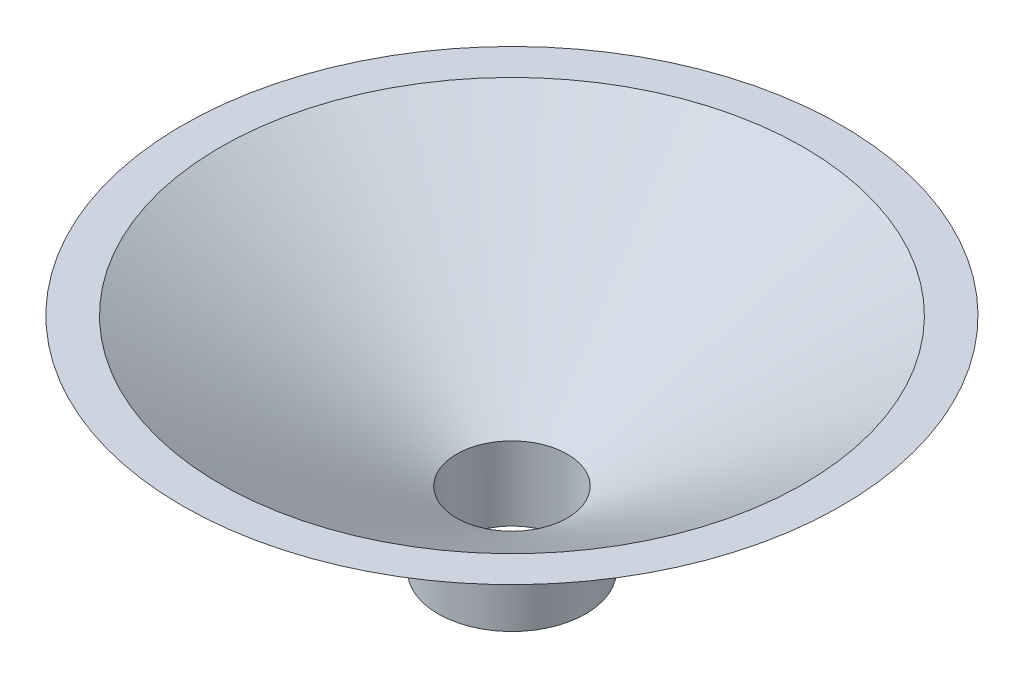
SolidWorks part; units mm, degrees
ref_plane "Front Plane" through (0, 0, 0) normal (0, 0, 1) x (1, 0, 0)
ref_plane "Top Plane" through (0, 0, 0) normal (0, 1, 0) x (1, 0, 0)
ref_plane "Right Plane" through (0, 0, 0) normal (1, 0, 0) x (0, 0, -1)
sketch "Sketch1" plane through (0, 0, 0) normal (0, 1, 0) x (1, 0, 0)
  circle A0 centre (0, 0) radius 7.5
  circle A1 centre (0, 0) radius 10
  dimension "D1" = 15
  dimension "D2" = 20
extrude "Boss-Extrude1" add sketch "Sketch1" along normal blind 10
sketch "Sketch6" plane through (0, 10, 0) normal (0, 1, 0) x (1, 0, 0)
  circle A0 centre (0, 0) radius 10
extrude "Boss-Extrude3" add sketch "Sketch6" along normal blind 20 draft 60 draft outward yes
sketch "Sketch8" plane through (0, 10, 0) normal (0, -1, 0) x (1, 0, 0)
  circle A0 centre (0, 0) radius 7.5
extrude "Cut-Extrude3" cut sketch "Sketch8" against normal blind 20 draft 58 draft outward yes
